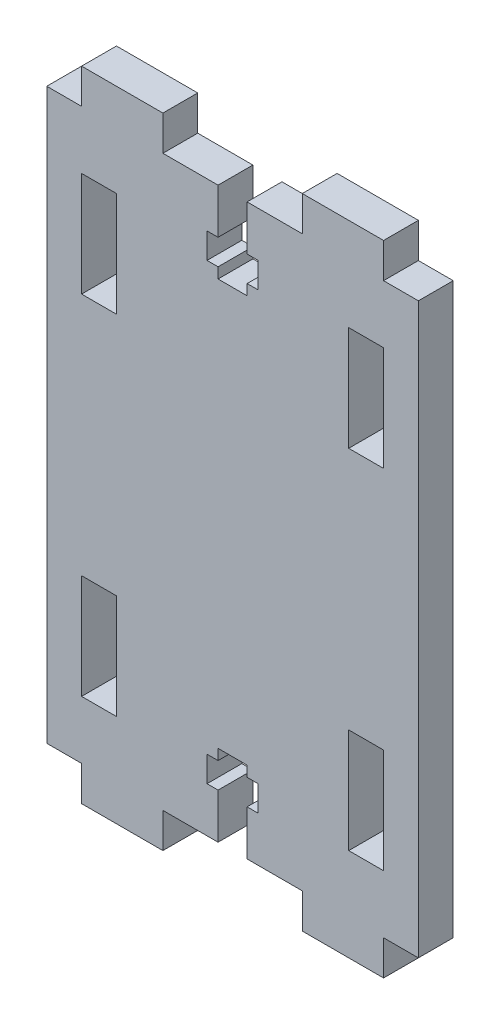
SolidWorks part; units mm, degrees
ref_plane "정면" through (0, 0, 0) normal (0, 0, 1) x (1, 0, 0)
ref_plane "윗면" through (0, 0, 0) normal (0, 1, 0) x (1, 0, 0)
ref_plane "우측면" through (0, 0, 0) normal (1, 0, 0) x (0, 0, -1)
sketch "스케치1" plane through (0, 0, 0) normal (0, 0, 1) x (1, 0, 0)
  line L1 (0, 0) -> (32, 0)
  line L2 (0, 0) -> (0, 55)
  line L3 (0, 55) -> (32, 55)
  line L4 (32, 0) -> (32, 55)
  dimension "D1" = 32
  dimension "D2" = 55
extrude "보스-돌출1" add sketch "스케치1" along normal blind 3
sketch "스케치2" plane through (0, 0, 3) normal (0, 0, 1) x (1, 0, 0)
  line L0 (0, 55) -> (0, 0) construction
  line L1 (0, 52) -> (3, 52)
  line L2 (0, 52) -> (0, 55)
  line L3 (0, 55) -> (32, 55)
  line L4 (32, 52) -> (32, 55)
  line L5 (10, 52) -> (22, 52)
  line L6 (3, 55) -> (10, 55)
  line L7 (3, 55) -> (3, 52)
  line L9 (10, 55) -> (10, 52)
  line L10 (22, 55) -> (29, 55)
  line L11 (22, 55) -> (22, 52)
  line L13 (29, 55) -> (29, 52)
  line L14 (29, 52) -> (32, 52)
  line L15 (-8.641, 27.5) -> (40.29, 27.5) construction
  line L16 (32, 3) -> (32, 0)
  line L17 (29, 3) -> (32, 3)
  line L18 (29, 0) -> (29, 3)
  line L19 (22, 0) -> (22, 3)
  line L20 (10, 3) -> (22, 3)
  line L21 (10, 0) -> (10, 3)
  line L22 (3, 0) -> (3, 3)
  line L23 (0, 3) -> (3, 3)
  line L24 (0, 3) -> (0, 0)
  line L25 (0, 0) -> (32, 0)
  point P15 (10, 53.5)
  line M12 (0, 55) -> (0, 0)
  line M13 (0, 0) -> (32, 0)
  line M14 (32, 0) -> (32, 55)
  line M15 (32, 55) -> (0, 55)
  dimension "D1" = 3
  dimension "D2" = 3
  dimension "D3" = 7
  dimension "D4" = 3
  dimension "D5" = 7
extrude "컷-돌출1" cut sketch "스케치2" against normal through all contours L7 L1 M15 M12 | L11 L9 L5 M15 | L13 L14 M14 M15 | L23 L22 M12 M13 | L21 L19 L20 M13 | L18 L17 M13 M14
sketch "스케치3" plane through (0, 0, 3) normal (0, 0, 1) x (1, 0, 0)
  line L0 (-4.7097, 27.5) -> (41.343, 27.5) construction
  line L1 (16, 54.7034) -> (16, 0) construction
  line L2 (0, 52) -> (3, 52) construction
  line L3 (3, 47) -> (6, 47)
  line L4 (3, 47) -> (3, 38)
  line L5 (3, 38) -> (6, 38)
  line L6 (6, 47) -> (6, 38)
  line L7 (29, 38) -> (26, 38)
  line L8 (26, 47) -> (26, 38)
  line L9 (29, 47) -> (26, 47)
  line L10 (29, 47) -> (29, 38)
  line L11 (29, 8) -> (29, 17)
  line L12 (29, 8) -> (26, 8)
  line L13 (26, 8) -> (26, 17)
  line L14 (29, 17) -> (26, 17)
  line L15 (3, 17) -> (6, 17)
  line L16 (6, 8) -> (6, 17)
  line L17 (3, 8) -> (6, 8)
  line L18 (3, 8) -> (3, 17)
  dimension "D1" = 3
  dimension "D2" = 9
  dimension "D3" = 5
extrude "컷-돌출2" cut sketch "스케치3" against normal through all
sketch "스케치5" plane through (0, 0, 3) normal (0, 0, 1) x (1, 0, 0)
  line L0 (10, 3) -> (22, 3) construction
  line L1 (14.75, 10) -> (17.25, 10)
  line L2 (14.75, 10) -> (14.75, 9.0884)
  line L3 (14.75, 3) -> (17.25, 3)
  line L4 (17.25, 10) -> (17.25, 9.0884)
  line L5 (0, 52) -> (0, 3) construction
  line L6 (17.25, 9.0884) -> (18.2, 9.0884)
  line L7 (13.8, 9.0884) -> (14.75, 9.0884)
  line L8 (13.8, 9.0884) -> (13.8, 6.8884)
  line L9 (13.8, 6.8884) -> (14.75, 6.8884)
  line L10 (18.2, 9.0884) -> (18.2, 6.8884)
  line L11 (14.75, 6.8884) -> (14.75, 3)
  line L12 (17.25, 6.8884) -> (18.2, 6.8884)
  line L13 (17.25, 6.8884) -> (17.25, 3)
  line L14 (-6.3581, 27.5) -> (44.5117, 27.5) construction
  line L15 (14.75, 45) -> (14.75, 45.9116)
  line L16 (13.8, 45.9116) -> (14.75, 45.9116)
  line L17 (13.8, 45.9116) -> (13.8, 48.1116)
  line L18 (13.8, 48.1116) -> (14.75, 48.1116)
  line L19 (14.75, 48.1116) -> (14.75, 52)
  line L20 (14.75, 52) -> (17.25, 52)
  line L21 (17.25, 48.1116) -> (17.25, 52)
  line L22 (17.25, 48.1116) -> (18.2, 48.1116)
  line L23 (18.2, 45.9116) -> (18.2, 48.1116)
  line L24 (17.25, 45.9116) -> (18.2, 45.9116)
  line L25 (17.25, 45) -> (17.25, 45.9116)
  line L26 (14.75, 45) -> (17.25, 45)
  dimension "D1" = 2.5
  dimension "D2" = 7
  dimension "D3" = 14.75
  dimension "D4" = 2.2
  dimension "D5" = 4.4
  dimension "D6" = 13.8
extrude "컷-돌출3" cut sketch "스케치5" against normal blind 10
